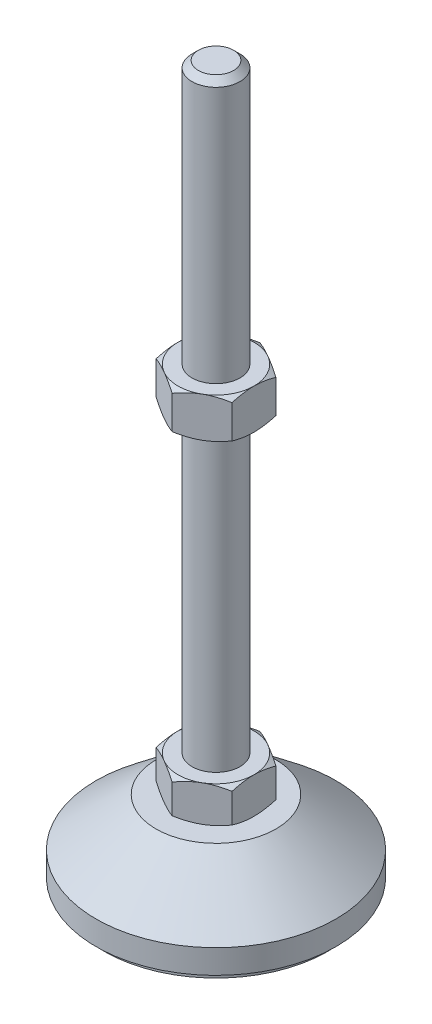
SolidWorks part; units mm, degrees
ref_plane "Спереди" through (0, 0, 0) normal (0, 0, 1) x (1, 0, 0)
ref_plane "Сверху" through (0, 0, 0) normal (0, 1, 0) x (1, 0, 0)
ref_plane "Справа" through (0, 0, 0) normal (1, 0, 0) x (0, 0, -1)
sketch "Эскиз1" plane through (0, 0, 0) normal (0, 0, 1) x (1, 0, 0)
  line L0 (0, 0) -> (-28, 0)
  line L1 (-28, 0) -> (-28, 2)
  line L2 (-28, 2) -> (-30, 2)
  line L3 (-30, 2) -> (-30, 8)
  line L4 (-30, 8) -> (-15, 20)
  line L5 (-15, 20) -> (-6, 20)
  line L12 (-6, 29) -> (-6, 177.4)
  line L13 (-6, 177.4) -> (-4.4, 179)
  line L14 (-4.4, 179) -> (0, 179)
  line L15 (0, 179) -> (0, 0) construction
  line L16 (-6, 20) -> (0, 20) construction
  line L17 (0, 0) -> (0, 179)
  line L18 (0, 0) -> (0, -7.9595) construction
  line L19 (-6, 29) -> (-6, 20)
  point P8 (-6, 103.2)
  point P23 (-10.5, 20)
  dimension "D1" = 12
  dimension "D2" = 20
  dimension "D3" = 9
  dimension "D4" = 60
  dimension "D5" = 6
  dimension "D6" = 1.6
  dimension "D7" = 45
  dimension "D8" = 30
  dimension "D9" = 2
  dimension "D10" = 150
  dimension "D11" = 6
revolve "Повернуть1" add sketch "Эскиз1" angle 360 about L17
sketch "Эскиз2" plane through (0, 20, 0) normal (0, 1, 0) x (1, 0, 0)
  line L1 (0, 10.9697) -> (-9.5, 5.4848)
  line L2 (-9.5, 5.4848) -> (-9.5, -5.4848)
  line L3 (-9.5, -5.4848) -> (0, -10.9697)
  line L4 (0, -10.9697) -> (9.5, -5.4848)
  line L5 (9.5, -5.4848) -> (9.5, 5.4848)
  line L6 (9.5, 5.4848) -> (0, 10.9697)
  circle A0 centre (0, 0) radius 9.5 construction
  dimension "D1" = 19
extrude "Бобышка-Вытянуть1" add sketch "Эскиз2" along normal up to vertex (9 mm away) up to point (-6, 29, 0)
ref_plane "Плоскость1" through (0, 103.2, 0) normal (0, 1, 0) x (1, 0, 0)
sketch "Эскиз3" plane through (0, 103.2, 0) normal (0, 1, 0) x (1, 0, 0)
  line L6 (9.5, 5.4848) -> (0, 10.9697)
  line L7 (0, 10.9697) -> (-9.5, 5.4848)
  line L8 (-9.5, 5.4848) -> (-9.5, -5.4848)
  line L9 (-9.5, -5.4848) -> (0, -10.9697)
  line L10 (0, -10.9697) -> (9.5, -5.4848)
  line L11 (9.5, -5.4848) -> (9.5, 5.4848)
  line L12 (9.5, 5.4848) -> (0, 10.9697)
  line L13 (0, 10.9697) -> (-9.5, 5.4848)
  line L14 (-9.5, 5.4848) -> (-9.5, -5.4848)
  line L15 (-9.5, -5.4848) -> (0, -10.9697)
  line L16 (0, -10.9697) -> (9.5, -5.4848)
  line L17 (9.5, -5.4848) -> (9.5, 5.4848)
  dimension "D1" = 0
extrude "Бобышка-Вытянуть2" add sketch "Эскиз3" along normal blind 10
sketch "Эскиз4" plane through (0, 0, 0) normal (0, 0, 1) x (1, 0, 0)
  line L0 (-9.5, 113.2) -> (-18.1603, 108.2)
  line L1 (-18.1603, 108.2) -> (-18.1603, 113.2)
  line L2 (-18.1603, 113.2) -> (-9.5, 113.2)
  line L3 (-18.1603, 108.2) -> (-9.5, 103.2)
  line L4 (50, 103.2) -> (-50, 103.2) construction
  line L5 (-9.5, 103.2) -> (-18.1603, 103.2)
  line L6 (-18.1603, 103.2) -> (-18.1603, 108.2)
  line L7 (-9.5, 113.2) -> (-9.5, 103.2) construction
  line L8 (-9.5, 29) -> (-17.2942, 29)
  line L9 (-17.2942, 29) -> (-17.2942, 24.5)
  line L10 (-17.2942, 24.5) -> (-9.5, 29)
  line L11 (-9.5, 20) -> (-17.2942, 24.5)
  line L12 (-17.2942, 24.5) -> (-17.2942, 20)
  line L13 (-17.2942, 20) -> (-9.5, 20)
  line L14 (0, 179) -> (0, 96.3793) construction
  dimension "D1" = 30
  dimension "D2" = 30
revolve "Вырез-Повернуть2" cut sketch "Эскиз4" angle 360 about L14
